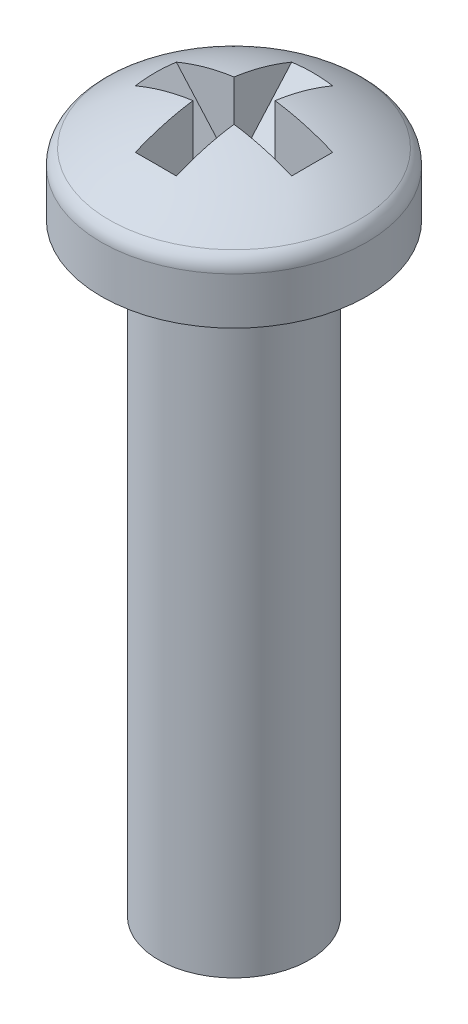
SolidWorks part; units mm, degrees
ref_plane "Plane1" through (0, 0, 0) normal (0, 0, 1) x (1, 0, 0)
ref_plane "Plane2" through (0, 0, 0) normal (0, 1, 0) x (1, 0, 0)
ref_plane "Plane3" through (0, 0, 0) normal (1, 0, 0) x (0, 0, -1)
sketch "Sketch1" plane through (0, 0, 0) normal (0, 0, 1) x (1, 0, 0)
  line L0 (0, 0) -> (2.794, 0)
  line L1 (2.794, 0) -> (2.794, 0.9881)
  line L2 (0, 2.2496) -> (0, 0)
  line L3 (0, 0) -> (0, 101.6) construction
  arc A0 (2.794, 0.9881) -> (2.6274, 1.3118) centre (2.3962, 0.9881) ccw
  arc A1 (2.6274, 1.3118) -> (0, 2.2496) centre (-0.3343, -2.8362) ccw
  dimension "D1" = 2.794
revolve "Base-Revolve" add sketch "Sketch1" angle 360 about L3
sketch "Sketch2" plane through (0, 0, 0) normal (0, 0, 1) x (1, 0, 0)
  line L0 (0, 0) -> (0, 101.6) construction
  line L1 (0, -12.7) -> (1.5875, -12.7)
  line L2 (1.5875, -12.7) -> (1.5875, 0)
  line L3 (1.5875, 0) -> (0, 0)
  line L4 (0, 0) -> (0, -12.7)
revolve "Boss-Revolve1" add sketch "Sketch2" angle 360 about L0
cosmetic thread "Cosmetic Thread1"
sketch "Sketch3" plane through (0, 0, 0) normal (0, 0, 1) x (1, 0, 0)
  line L0 (-2.0193, 3.3909) -> (2.0193, 3.3909)
  line L1 (2.0193, 3.3909) -> (2.0193, 2.2606)
  line L2 (2.0193, 2.2606) -> (0, -0.0254)
  line L3 (0, -0.0254) -> (-2.0193, 2.2606)
  line L4 (-2.0193, 2.2606) -> (-2.0193, 3.3909)
extrude "Cut-Extrude1" cut sketch "Sketch3" against normal mid plane 0.8636
sketch "Sketch4" plane through (0, 0, 0) normal (1, 0, 0) x (0, 0, -1)
  line L0 (-2.0193, 3.3909) -> (2.0193, 3.3909)
  line L1 (2.0193, 3.3909) -> (2.0193, 2.2606)
  line L2 (2.0193, 2.2606) -> (0, -0.0254)
  line L3 (0, -0.0254) -> (-2.0193, 2.2606)
  line L4 (-2.0193, 2.2606) -> (-2.0193, 3.3909)
extrude "Cut-Extrude2" cut sketch "Sketch4" against normal mid plane 0.8636
